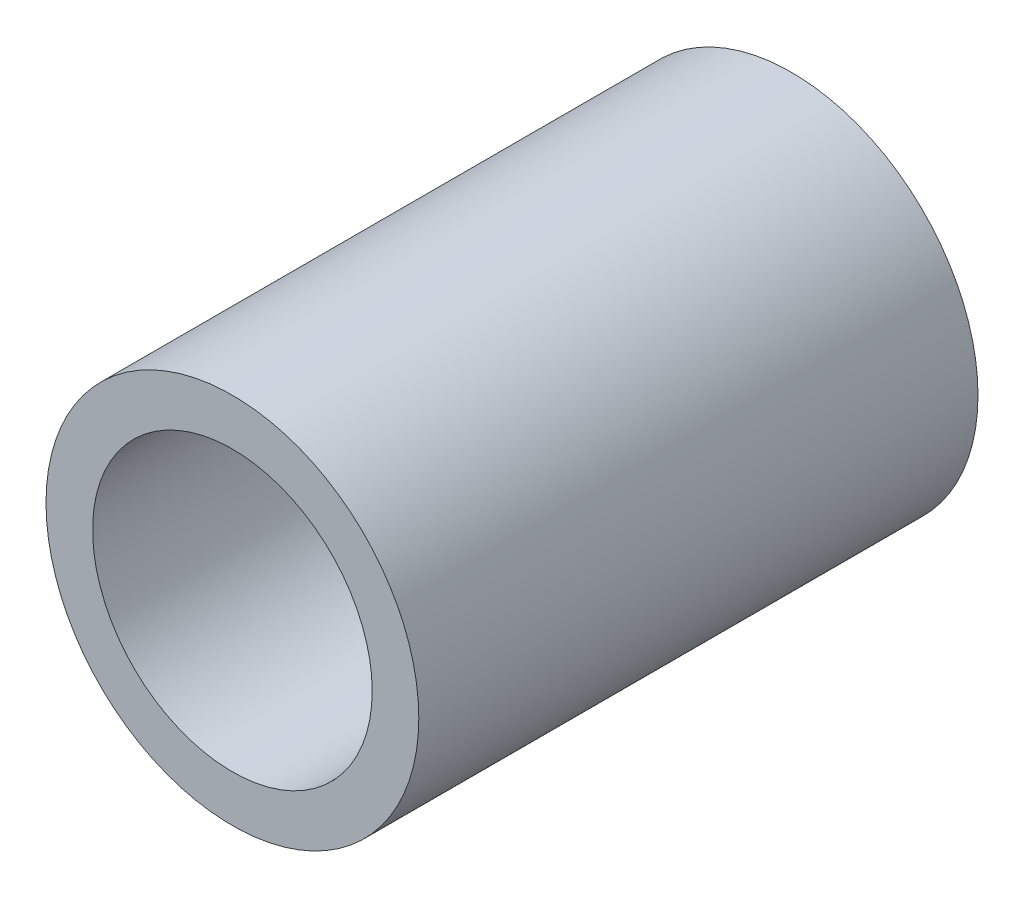
SolidWorks part; units mm, degrees
ref_plane "Front Plane" through (0, 0, 0) normal (0, 0, 1) x (1, 0, 0)
ref_plane "Top Plane" through (0, 0, 0) normal (0, 1, 0) x (1, 0, 0)
ref_plane "Right Plane" through (0, 0, 0) normal (1, 0, 0) x (0, 0, -1)
sketch "Sketch1" plane through (0, 0, 0) normal (0, 0, 1) x (1, 0, 0)
  line L0 (0, 0) -> (27.5257, 0) construction
  line L1 (0, 0) -> (0, 26.121) construction
  circle A0 centre (0, 0) radius 20
extrude "Boss-Extrude1" add sketch "Sketch1" along normal blind 60
sketch "Sketch2" plane through (0, 0, 60) normal (0, 0, 1) x (1, 0, 0)
  circle A0 centre (0, 0) radius 15
extrude "Cut-Extrude1" cut sketch "Sketch2" against normal blind 58
